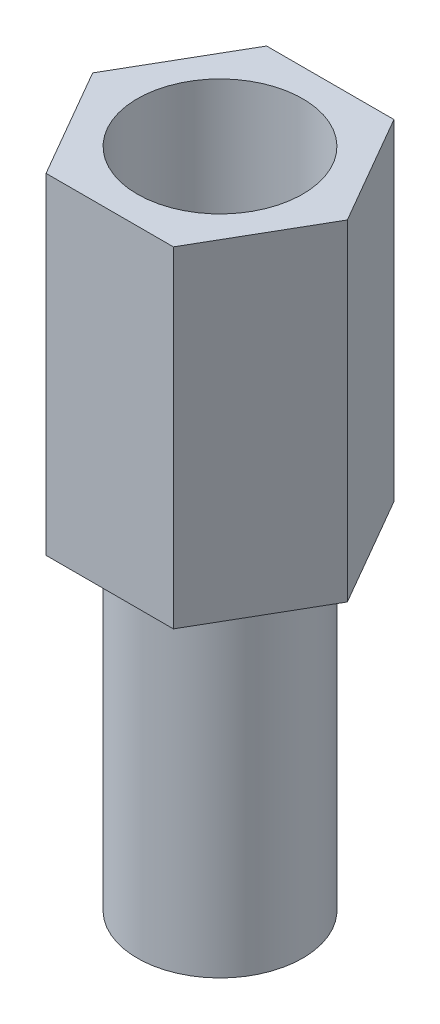
SolidWorks part; units mm, degrees
material "Brass"
ref_plane "Front Plane" through (0, 0, 0) normal (0, 0, 1) x (1, 0, 0)
ref_plane "Top Plane" through (0, 0, 0) normal (0, 1, 0) x (1, 0, 0)
ref_plane "Right Plane" through (0, 0, 0) normal (1, 0, 0) x (0, 0, -1)
sketch "Sketch2" plane through (0, 0, 0) normal (0, 1, 0) x (1, 0, 0)
  line L1 (1.1547, 2) -> (-1.1547, 2)
  line L2 (-1.1547, 2) -> (-2.3094, 0)
  line L3 (-2.3094, 0) -> (-1.1547, -2)
  line L4 (-1.1547, -2) -> (1.1547, -2)
  line L5 (1.1547, -2) -> (2.3094, 0)
  line L6 (2.3094, 0) -> (1.1547, 2)
  circle A0 centre (0, 0) radius 1.5
  circle A1 centre (0, 0) radius 2 construction
  point P3 (0, 2)
  point P11 (0, 1.5)
  dimension "D1" = 3
  dimension "D2" = 0.5
extrude "Boss-Extrude1" add sketch "Sketch2" along normal blind 6
sketch "Sketch3" plane through (0, 0, 0) normal (0, -1, 0) x (1, 0, 0)
  circle A0 centre (0, 0) radius 1.5
extrude "Boss-Extrude2" add sketch "Sketch3" along normal blind 6 separate body
